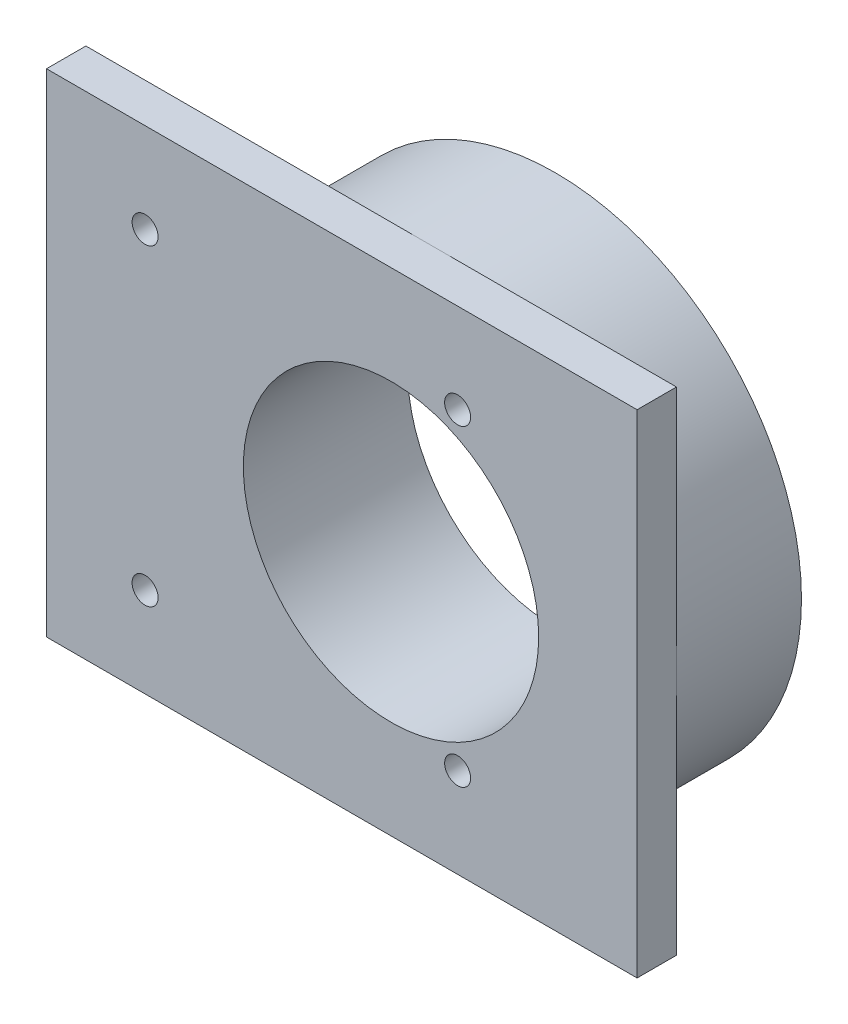
SolidWorks part; units mm, degrees
ref_plane "Front Plane" through (0, 0, 0) normal (0, 0, 1) x (1, 0, 0)
ref_plane "Top Plane" through (0, 0, 0) normal (0, 1, 0) x (1, 0, 0)
ref_plane "Right Plane" through (0, 0, 0) normal (1, 0, 0) x (0, 0, -1)
sketch "Sketch1" plane through (0, 0, 0) normal (0, 0, 1) x (1, 0, 0)
  circle A0 centre (0, 0) radius 25
  dimension "D1" = 50
extrude "Boss-Extrude1" add sketch "Sketch1" along normal blind 12.7
sketch "Sketch2" plane through (0, 0, 12.7) normal (0, 0, 1) x (1, 0, 0)
  line L1 (-35, 25) -> (25, 25)
  line L2 (-35, 25) -> (-35, -25)
  line L3 (-35, -25) -> (25, -25)
  line L4 (25, 25) -> (25, -25)
  line L6 (0, 0) -> (0, 16.6497) construction
  dimension "D1" = 25
  dimension "D2" = 25
  dimension "D3" = 35
  dimension "D4" = 25
extrude "Boss-Extrude2" add sketch "Sketch2" along normal blind 4
sketch "Sketch3" plane through (0, 0, 16.7) normal (0, 0, 1) x (1, 0, 0)
  line L0 (-9.11, 15.875) -> (-9.11, 0) construction
  line L1 (-24.985, 15.875) -> (6.765, 15.875) construction
  line L2 (6.765, 15.875) -> (6.765, -15.875) construction
  line L3 (6.765, -15.875) -> (-24.985, -15.875) construction
  line L4 (-24.985, -15.875) -> (-24.985, 15.875) construction
  line L5 (-24.985, 15.875) -> (6.765, -15.875) construction
  line L6 (0.89, 0) -> (12.4661, 0) construction
  line L7 (0, 0) -> (0, -3.1013) construction
  circle A0 centre (-24.985, 15.875) radius 1.32
  circle A1 centre (6.765, 15.875) radius 1.32
  circle A2 centre (6.765, -15.875) radius 1.32
  circle A3 centre (-24.985, -15.875) radius 1.32
  dimension "D1" = 2.64
  dimension "D6" = 9.11
  dimension "D4" = 31.75
  dimension "D5" = 31.75
  dimension "D2" = 2
  dimension "D3" = 2
extrude "Cut-Extrude1" cut sketch "Sketch3" against normal through all
sketch "Sketch4" plane through (0, 0, 16.7) normal (0, 0, 1) x (1, 0, 0)
  circle A0 centre (0, 0) radius 15
  dimension "D1" = 30
extrude "Cut-Extrude2" cut sketch "Sketch4" against normal through all
